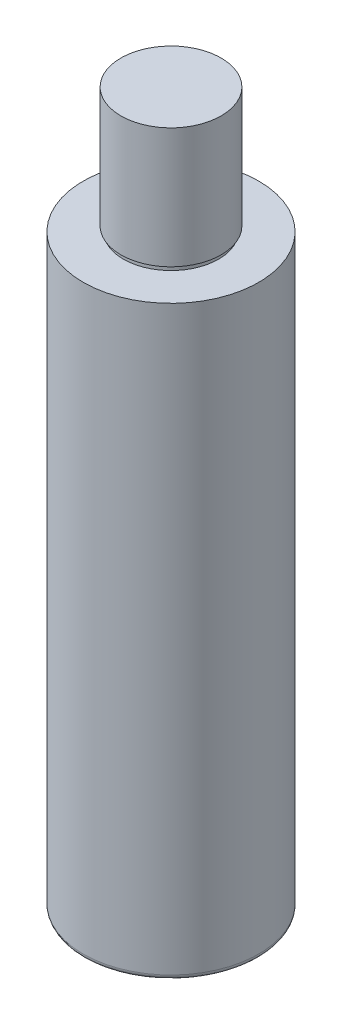
SolidWorks part; units mm, degrees
ref_plane "Front Plane" through (0, 0, 0) normal (0, 0, 1) x (1, 0, 0)
ref_plane "Top Plane" through (0, 0, 0) normal (0, 1, 0) x (1, 0, 0)
ref_plane "Right Plane" through (0, 0, 0) normal (1, 0, 0) x (0, 0, -1)
sketch "Sketch1" plane through (0, 0, 0) normal (0, 1, 0) x (1, 0, 0)
  circle A0 centre (0, 0) radius 17.5
extrude "Boss-Extrude1" add sketch "Sketch1" along normal blind 142 separate body
sketch "Sketch2" plane through (0, 142, 0) normal (0, 1, 0) x (1, 0, 0)
  circle A0 centre (0, 0) radius 10
extrude "Cut-Extrude1" cut sketch "Sketch2" against normal blind 25 flip side to cut
sketch "Sketch3" plane through (0, 117, 0) normal (0, 1, 0) x (1, 0, 0)
  circle A0 centre (0, 0) radius 9.5
extrude "Cut-Extrude2" cut sketch "Sketch3" along normal blind 1 flip side to cut
fillet "Fillet1" radius 1 1 edges at (0, 0, 17.5)
